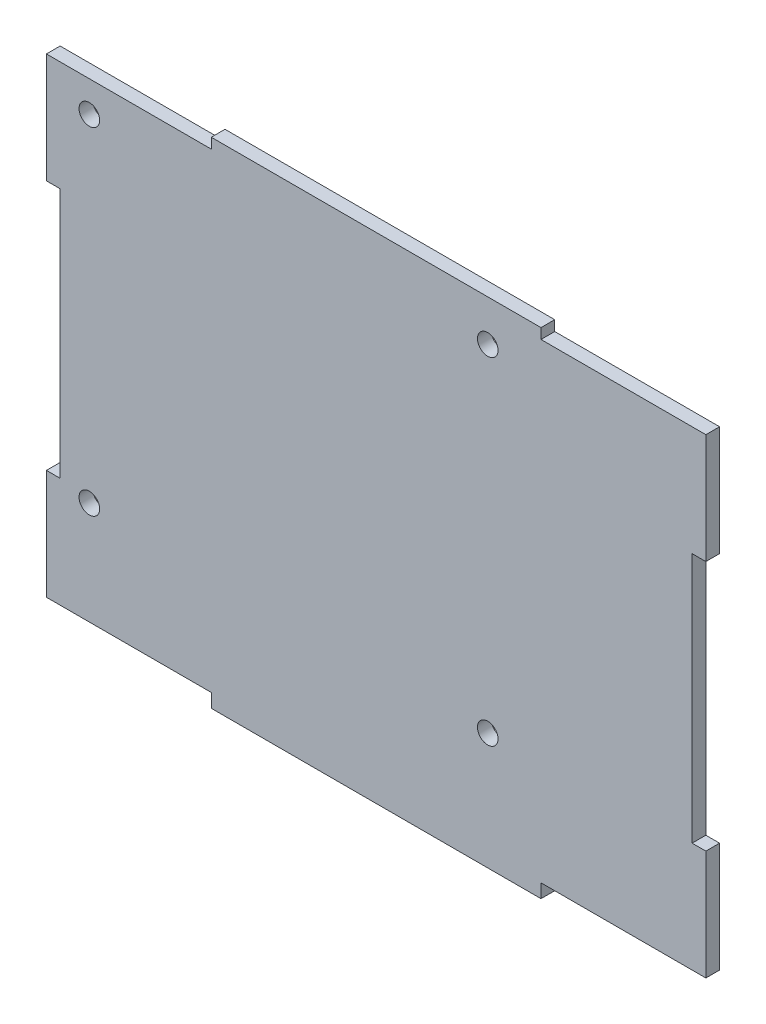
SolidWorks part; units mm, degrees
ref_plane "正面" through (0, 0, 0) normal (0, 0, 1) x (1, 0, 0)
ref_plane "平面" through (0, 0, 0) normal (0, 1, 0) x (1, 0, 0)
ref_plane "右側面" through (0, 0, 0) normal (1, 0, 0) x (0, 0, -1)
sketch "ｽｹｯﾁ1" plane through (0, 0, 0) normal (0, 0, 1) x (1, 0, 0)
  line L1 (-45.9728, 49.5738) -> (50.0272, 49.5738)
  line L2 (-45.9728, 49.5738) -> (-45.9728, -22.4262)
  line L3 (-45.9728, -22.4262) -> (50.0272, -22.4262)
  line L4 (50.0272, 49.5738) -> (50.0272, -22.4262)
  dimension "D1" = 96
  dimension "D2" = 72
extrude "ﾎﾞｽ - 押し出し1" add sketch "ｽｹｯﾁ1" along normal blind 2
sketch "ｽｹｯﾁ2" plane through (0, 0, 0) normal (0, 0, -1) x (-1, 0, 0)
  circle A0 centre (-18.2772, -5.4262) radius 1.5
  circle A1 centre (-18.2772, 43.5738) radius 1.5
  circle A2 centre (39.7228, -5.4262) radius 1.5
  circle A3 centre (39.7228, 43.5738) radius 1.5
  dimension "D1" = 3
extrude "ｶｯﾄ - 押し出し1" cut sketch "ｽｹｯﾁ2" against normal through all
sketch "ｽｹｯﾁ3" plane through (0, 0, 0) normal (0, 0, -1) x (-1, 0, 0)
  line L0 (45.9728, -20.4262) -> (21.9728, -20.4262) construction
  line L1 (45.9728, -22.4262) -> (21.9728, -22.4262)
  line L2 (45.9728, -22.4262) -> (45.9728, -20.4262)
  line L3 (45.9728, -20.4262) -> (21.9728, -20.4262)
  line L4 (21.9728, -22.4262) -> (21.9728, -20.4262)
  line L6 (-50.0272, -22.4262) -> (-26.0272, -22.4262)
  line L7 (-50.0272, -22.4262) -> (-50.0272, -20.4262)
  line L8 (-50.0272, -20.4262) -> (-26.0272, -20.4262)
  line L9 (-26.0272, -22.4262) -> (-26.0272, -20.4262)
  dimension "D1" = 24
  dimension "D2" = 24
extrude "ｶｯﾄ - 押し出し2" cut sketch "ｽｹｯﾁ3" against normal through all
sketch "ｽｹｯﾁ4" plane through (0, 0, 0) normal (0, 0, -1) x (-1, 0, 0)
  line L0 (45.9728, 48.0738) -> (21.9728, 48.0738) construction
  line L1 (45.9728, 50.0738) -> (21.9728, 50.0738)
  line L2 (45.9728, 50.0738) -> (45.9728, 48.0738)
  line L3 (45.9728, 48.0738) -> (21.9728, 48.0738)
  line L4 (21.9728, 50.0738) -> (21.9728, 48.0738)
  line L6 (-50.0272, 50.0738) -> (-26.0272, 50.0738)
  line L7 (-50.0272, 50.0738) -> (-50.0272, 48.0738)
  line L8 (-50.0272, 48.0738) -> (-26.0272, 48.0738)
  line L9 (-26.0272, 50.0738) -> (-26.0272, 48.0738)
  dimension "D1" = 24
  dimension "D2" = 24
extrude "ｶｯﾄ - 押し出し3" cut sketch "ｽｹｯﾁ4" against normal through all
sketch "ｽｹｯﾁ5" plane through (0, 0, 0) normal (0, 0, -1) x (-1, 0, 0)
  line L1 (45.9728, -4.4262) -> (43.9728, -4.4262)
  line L2 (45.9728, -4.4262) -> (45.9728, 32.0738)
  line L3 (45.9728, 32.0738) -> (43.9728, 32.0738)
  line L4 (43.9728, -4.4262) -> (43.9728, 32.0738)
extrude "ｶｯﾄ - 押し出し4" cut sketch "ｽｹｯﾁ5" against normal through all
sketch "ｽｹｯﾁ6" plane through (0, 0, 0) normal (0, 0, -1) x (-1, 0, 0)
  line L1 (-50.0272, -4.4262) -> (-48.0272, -4.4262)
  line L2 (-50.0272, -4.4262) -> (-50.0272, 32.0738)
  line L3 (-50.0272, 32.0738) -> (-48.0272, 32.0738)
  line L4 (-48.0272, -4.4262) -> (-48.0272, 32.0738)
extrude "ｶｯﾄ - 押し出し5" cut sketch "ｽｹｯﾁ6" against normal through all
